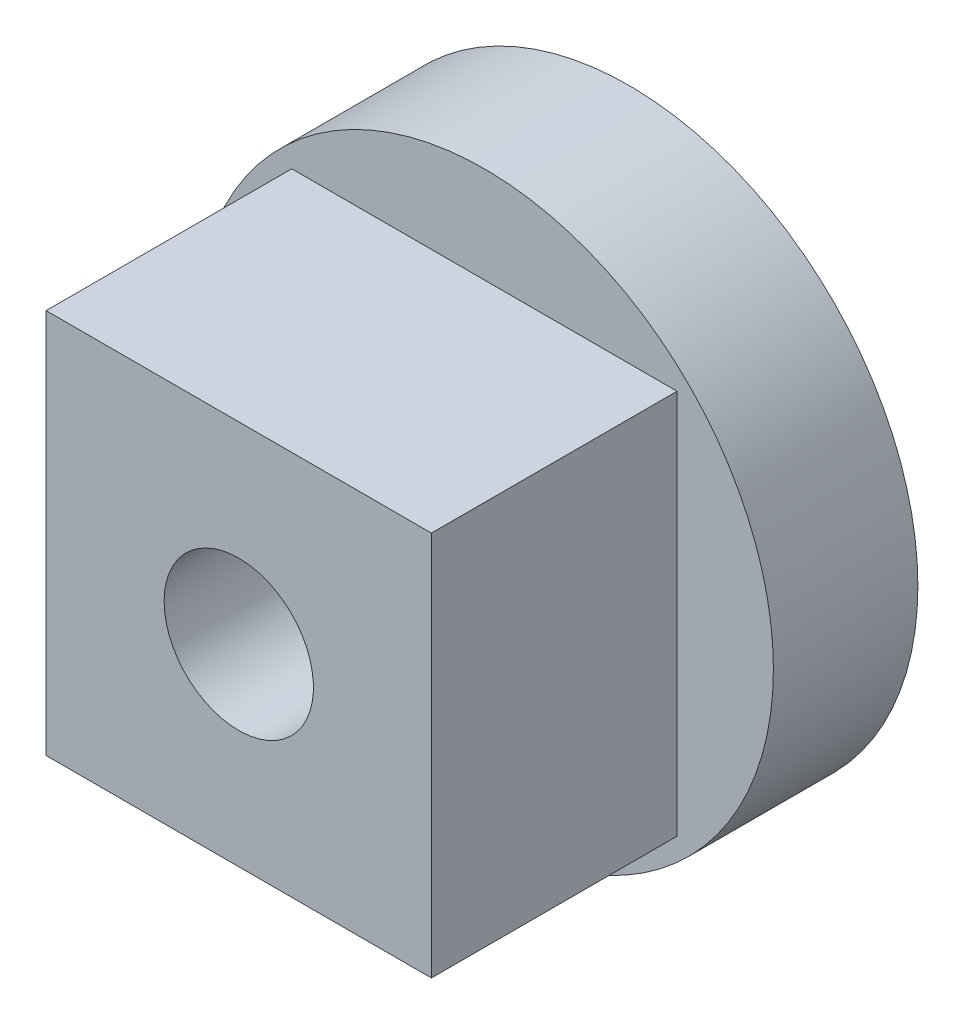
SolidWorks part; units mm, degrees
ref_plane "前视基准面" through (0, 0, 0) normal (0, 0, 1) x (1, 0, 0)
ref_plane "上视基准面" through (0, 0, 0) normal (0, 1, 0) x (1, 0, 0)
ref_plane "右视基准面" through (0, 0, 0) normal (1, 0, 0) x (0, 0, -1)
sketch "草图1" plane through (0, 0, 0) normal (0, 0, 1) x (1, 0, 0)
  circle A0 centre (0, 0) radius 6
  dimension "D1" = 12
extrude "凸台-拉伸1" add sketch "草图1" along normal blind 3
sketch "草图2" plane through (0, 0, 3) normal (0, 0, 1) x (1, 0, 0)
  line L1 (4, -4) -> (-4, -4)
  line L2 (4, -4) -> (4, 4)
  line L3 (4, 4) -> (-4, 4)
  line L4 (-4, -4) -> (-4, 4)
  line L5 (4, -4) -> (-4, 4) construction
  line L6 (4, 4) -> (-4, -4) construction
  point P0 (0, 0)
  dimension "D1" = 8
  dimension "D2" = 8
extrude "凸台-拉伸2" add sketch "草图2" along normal blind 5.1
sketch "草图4" plane through (0, 0, 0) normal (0, 0, -1) x (-1, 0, 0)
  circle A0 centre (0, 0) radius 2.85
  dimension "D1" = 5.7
extrude "切除-拉伸1" cut sketch "草图4" against normal blind 1
sketch "草图5" plane through (0, 0, 1) normal (0, 0, -1) x (-1, 0, 0)
  circle A0 centre (0, 0) radius 1.55
  dimension "D1" = 3.1
extrude "切除-拉伸2" cut sketch "草图5" against normal through all
